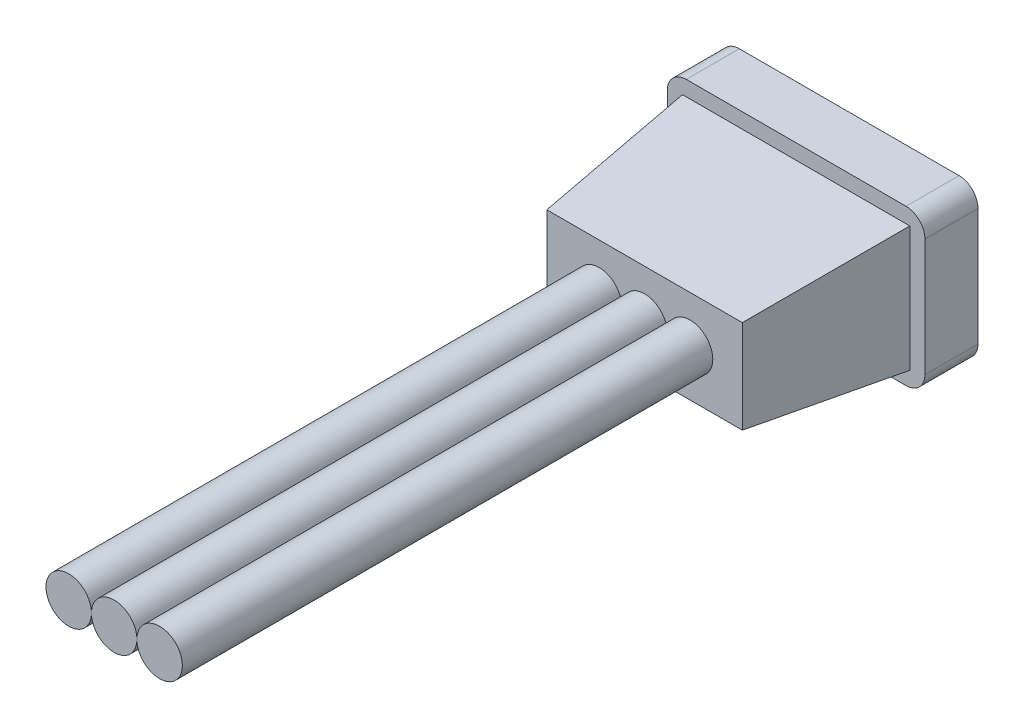
SolidWorks part; units mm, degrees
ref_plane "Front Plane" through (0, 0, 0) normal (0, 0, 1) x (1, 0, 0)
ref_plane "Top Plane" through (0, 0, 0) normal (0, 1, 0) x (1, 0, 0)
ref_plane "Right Plane" through (0, 0, 0) normal (1, 0, 0) x (0, 0, -1)
sketch "Sketch1" plane through (0, 0, 0) normal (0, 0, 1) x (1, 0, 0)
  line L1 (-3.4, 2.05) -> (3.4, 2.05)
  line L2 (-3.4, 2.05) -> (-3.4, -2.05)
  line L3 (-3.4, -2.05) -> (3.4, -2.05)
  line L4 (3.4, 2.05) -> (3.4, -2.05)
  line L5 (-3.4, 2.05) -> (3.4, -2.05) construction
  line L6 (-3.4, -2.05) -> (3.4, 2.05) construction
  point P0 (0, 0)
  dimension "D1" = 6.8
  dimension "D2" = 4.1
extrude "Boss-Extrude1" add sketch "Sketch1" along normal blind 1.4
sketch "Sketch2" plane through (0, 0, 1.4) normal (0, 0, 1) x (1, 0, 0)
  line L0 (-3.4, 2.05) -> (-3.4, -2.05) construction
  line L1 (-3, 1.65) -> (3, 1.65)
  line L2 (-3, 1.65) -> (-3, -1.65)
  line L3 (-3, -1.65) -> (3, -1.65)
  line L4 (3, 1.65) -> (3, -1.65)
  line L5 (-3, 1.65) -> (3, -1.65) construction
  line L6 (-3, -1.65) -> (3, 1.65) construction
  line L7 (3.4, 2.05) -> (-3.4, 2.05) construction
  point P0 (0, 0)
  dimension "D1" = 0.4
  dimension "D2" = 0.4
extrude "Boss-Extrude2" add sketch "Sketch2" along normal blind 4 draft 6
fillet "Fillet1" radius 0.5 4 edges at (-3.4, -2.05, 0.7) (-3.4, 2.05, 0.7) (3.4, -2.05, 0.7) (3.4, 2.05, 0.7)
sketch "Sketch3" plane through (0, 0, 5.4) normal (0, 0, 1) x (1, 0, 0)
  circle A0 centre (0, 0) radius 0.6
  dimension "D1" = 1.2
extrude "POSITIVE" add sketch "Sketch3" along normal blind 14 separate body
sketch "Sketch4" plane through (0, 0, 5.4) normal (0, 0, 1) x (1, 0, 0)
  line L0 (1.2, 0) -> (0, 0) construction
  circle A0 centre (1.2, 0) radius 0.6
  circle A1 centre (0, 0) radius 0.6 construction
extrude "SIGNAL" add sketch "Sketch4" along normal up to surface (14 mm away) separate body up to face at (0.6, 0, 19.4)
sketch "Sketch5" plane through (0, 0, 5.4) normal (0, 0, 1) x (1, 0, 0)
  line L0 (0, 0) -> (-1.2, 0) construction
  circle A0 centre (-1.2, 0) radius 0.6
  circle A1 centre (0, 0) radius 0.6 construction
extrude "NEGATIVE" add sketch "Sketch5" along normal up to surface (14 mm away) separate body up to face at (0.6, 0, 19.4)
